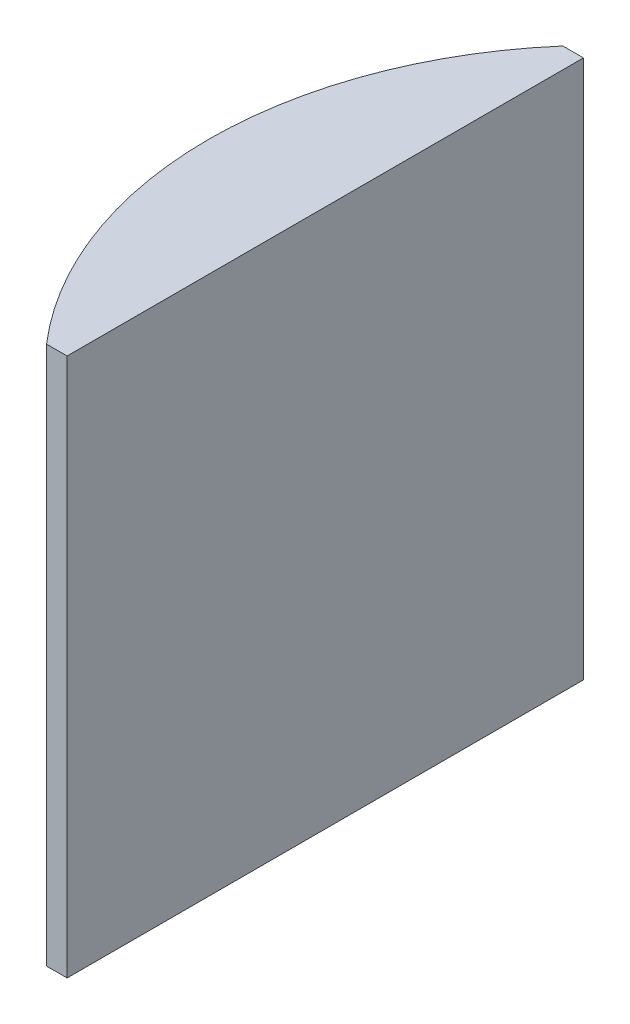
SolidWorks part; units mm, degrees
ref_plane "前视基准面" through (0, 0, 0) normal (0, 0, 1) x (1, 0, 0)
ref_plane "上视基准面" through (0, 0, 0) normal (0, 1, 0) x (1, 0, 0)
ref_plane "右视基准面" through (0, 0, 0) normal (1, 0, 0) x (0, 0, -1)
sketch "草图1" plane through (0, 0, 0) normal (0, 1, 0) x (1, 0, 0)
  line L0 (10.7432, 0) -> (-607.0701, 0) construction
  line L1 (-24.9489, 25.4) -> (-22.9248, 25.4)
  line L2 (-24.9489, -25.4) -> (-22.9248, -25.4)
  line L3 (-22.9248, 25.4) -> (-22.9248, -25.4)
  arc A0 (-24.9489, 25.4) -> (-24.9489, -25.4) centre (4.3552, 0) ccw
  point P19 (-34.4248, 0)
  point P20 (-22.9248, 0)
  dimension "D2" = 25.4
  dimension "D3" = 38.78
  dimension "D4" = 11.5
  dimension "D1" = 25.4
extrude "凸台-拉伸1" add sketch "草图1" along normal blind 53
